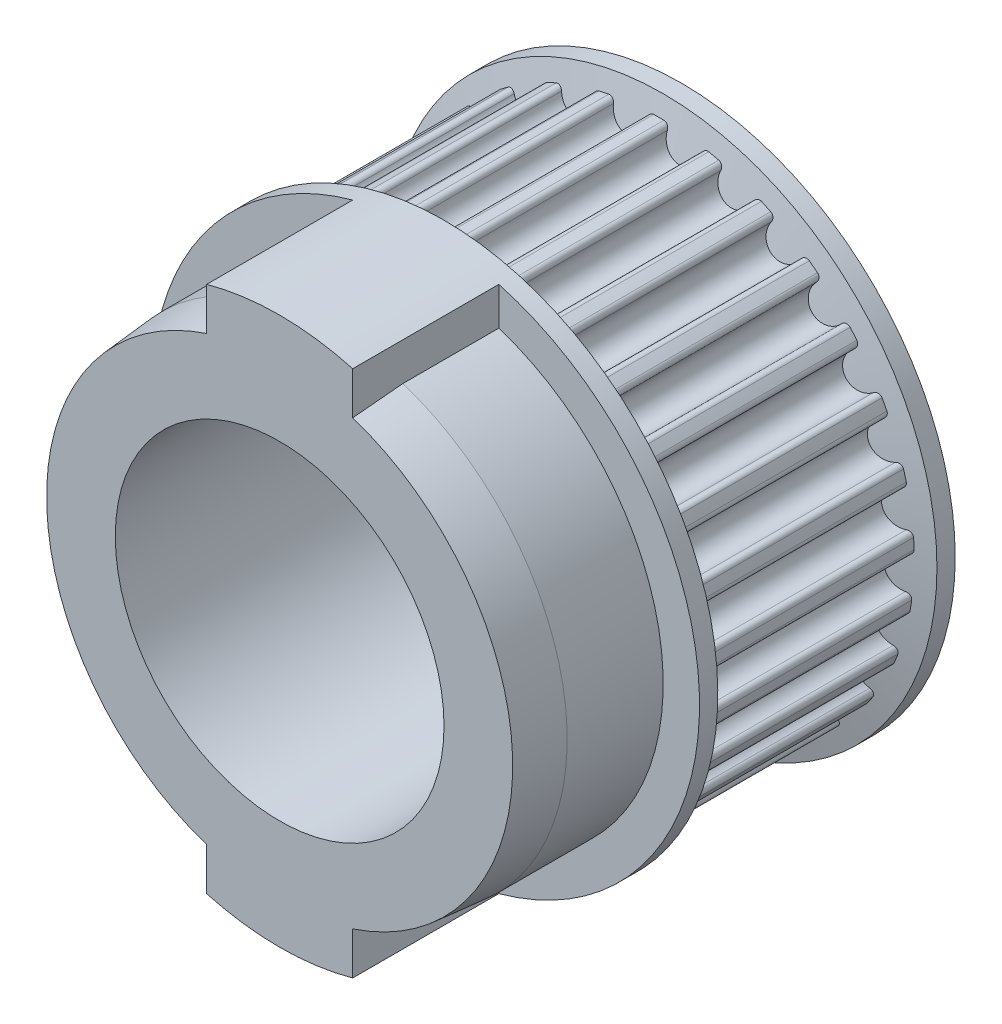
SolidWorks part; units mm, degrees
ref_plane "Front Plane" through (0, 0, 0) normal (0, 0, 1) x (1, 0, 0)
ref_plane "Top Plane" through (0, 0, 0) normal (0, 1, 0) x (1, 0, 0)
ref_plane "Right Plane" through (0, 0, 0) normal (1, 0, 0) x (0, 0, -1)
sketch "Sketch1" plane through (0, 0, 0) normal (0, 0, 1) x (1, 0, 0)
  circle A0 centre (0, 0) radius 23.0775
  dimension "D1" = 46.1549
extrude "Boss-Extrude1" add sketch "Sketch1" along normal mid plane 19.05
sketch "Sketch2" plane through (0, 0, 0) normal (0, 0, 1) x (1, 0, 0)
  line L0 (0, 0) -> (0, 22.2075) construction
  line L1 (0, 0) -> (2.3394, 21.5106) construction
  line L2 (0, 22.2075) -> (0, 23.0775)
  line L3 (2.3394, 21.5106) -> (2.4951, 22.9422) construction
  line L4 (4.7739, 21.6883) -> (4.961, 22.5379)
  arc A0 (0, 22.2075) -> (0.4461, 22.203) centre (0, 0) cw
  arc A1 (0.4461, 22.203) -> (0.8634, 21.7143) centre (0.4375, 21.7731) cw
  arc A2 (0.8634, 21.7143) -> (3.8247, 21.3922) centre (2.3394, 21.5106) ccw
  circle A3 centre (0, 0) radius 23.0775 construction
  arc A4 (0, 23.0775) -> (4.961, 22.5379) centre (0, 0) cw
  arc A5 (4.3373, 21.7798) -> (3.8247, 21.3922) centre (4.2533, 21.3581) ccw
  arc A6 (4.7739, 21.6883) -> (4.3373, 21.7798) centre (0, 0) ccw
  point P6 (2.1783, 20.0294)
  dimension "D1" = 0.43
  dimension "D2" = 1.49
  dimension "D3" = 0.87
  dimension "D4" = 6.207
  dimension "D5" = 2.93
extrude "Cut-Extrude1" cut sketch "Sketch2" against normal through all both and the other way through all
pattern_circular "CirPattern1" count 29 over 360 about axis through (0, 0, 0) along (0, 0, 1) of "Cut-Extrude1"
sketch "Sketch4" plane through (0, 0, 9.525) normal (0, 0, 1) x (1, 0, 0)
  circle A0 centre (0, 0) radius 23.795
  arc A1 (20.4609, -8.6326) -> (20.7912, -7.8038) centre (0, 0) ccw construction
  circle A2 centre (0, 0) radius 3.175
  dimension "D1" = 1.5875
  dimension "D2" = 6.35
extrude "Boss-Extrude2" add sketch "Sketch4" along normal blind 1.5875
sketch "Sketch3" plane through (0, 0, 11.1125) normal (0, 0, 1) x (1, 0, 0)
  circle A0 centre (0, 0) radius 3.175
  dimension "D1" = 6.35
extrude "Cut-Extrude2" cut sketch "Sketch3" against normal through all both and the other way through all
sketch "Sketch6" plane through (0, 0, 0) normal (0, 1, 0) x (1, 0, 0)
  line L0 (23.795, -9.525) -> (18.542, -8.255)
  line L1 (18.542, -8.255) -> (18.542, -9.525)
  line L2 (19.8525, -9.525) -> (17.627, -9.525) construction
  line L3 (18.542, -9.525) -> (23.795, -9.525)
  dimension "D1" = 18.542
  dimension "D2" = 1.27
ref_axis "Axis1" through (0, 0, -9.525) along (0, 0, 1)
revolve "Revolve1" add sketch "Sketch6" angle 360 about axis through (0, 0, -9.525) along (0, 0, 1)
mirror "Mirror1" about plane through (0, 0, 0) normal (0, 0, 1) of "Boss-Extrude2", "Revolve1"
sketch "Sketch8" plane through (0, 0, -11.1125) normal (0, 0, -1) x (-1, 0, 0)
  circle A0 centre (0, 0) radius 14.2875
  circle A1 centre (0, 0) radius 3.175 construction
  circle A2 centre (0, 0) radius 3.175
  dimension "D1" = 28.575
extrude "Cut-Extrude3" cut sketch "Sketch8" against normal through all
sketch "Sketch9" plane through (0, 0, 11.1125) normal (0, 0, 1) x (1, 0, 0)
  circle A0 centre (0, 0) radius 14.2875 construction
  circle A1 centre (0, 0) radius 14.2875
  circle A2 centre (0, 0) radius 20.6375
  dimension "D1" = 41.275
extrude "Boss-Extrude3" add sketch "Sketch9" along normal blind 12.7
chamfer "Chamfer1" distance 0.381 angle 85 1 edges at (20.6375, 0, 23.8125)
sketch "Sketch10" plane through (0, 0, 11.1125) normal (0, 0, 1) x (1, 0, 0)
  line L0 (0, 23.795) -> (0, 20.2565) construction
  line L1 (-6.35, 22.932) -> (-6.35, 19.2355)
  line L2 (6.35, 22.932) -> (6.35, 19.2355)
  line L3 (0, 22.0257) -> (-6.35, 22.0257) construction
  line L4 (0, 22.0257) -> (6.35, 22.0257) construction
  circle A0 centre (0, 0) radius 23.795 construction
  circle A1 centre (0, 0) radius 20.2565 construction
  arc A2 (6.35, 22.932) -> (-6.35, 22.932) centre (0, 0) ccw
  arc A3 (6.35, 19.2355) -> (-6.35, 19.2355) centre (0, 0) ccw
  dimension "D1" = 12.7
extrude "Boss-Extrude4" add sketch "Sketch10" along normal up to surface (12.7 mm away) up to face at (20.2565, 0, 23.8125)
mirror "Mirror2" about plane through (0, 0, 0) normal (0, 1, 0) of "Boss-Extrude4"
equation "\"n\" = 29'Number of Teeth"
equation "\"p\"= 5mm'Pitch"
equation "\"pd\"= \"n\" * \"p\" / pi'Pitch Diameter"
equation "\"D1@Sketch1\"=\"pd\""
equation "\"w\"= 0.75'Pulley Width"
equation "\"D1@Boss-Extrude1\"=\"w\""
equation "\"D4@Sketch2\"=180/\"n\""
equation "\"D1@CirPattern1\"=\"n\""
